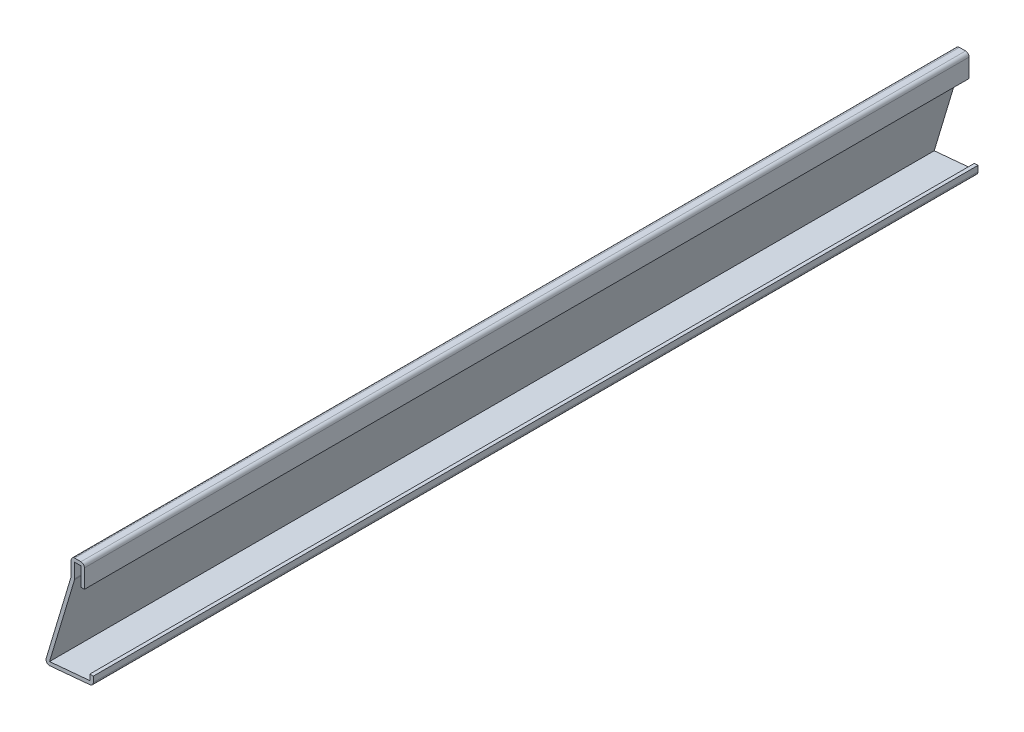
SolidWorks part; units mm, degrees
ref_plane "Front Plane" through (0, 0, 0) normal (0, 0, 1) x (1, 0, 0)
ref_plane "Top Plane" through (0, 0, 0) normal (0, 1, 0) x (1, 0, 0)
ref_plane "Right Plane" through (0, 0, 0) normal (1, 0, 0) x (0, 0, -1)
sketch "Sketch1" plane through (0, 0, 0) normal (0, 0, 1) x (1, 0, 0)
  line L0 (0, 4.7625) -> (0, 1.5875)
  line L1 (0, 1.5875) -> (-17.4625, 0)
  line L2 (-17.4625, 0) -> (-7.9375, 31.75)
  line L3 (-7.9375, 31.75) -> (-7.9375, 38.1)
  line L4 (-7.9375, 38.1) -> (-3.175, 38.1)
  line L5 (-3.175, 38.1) -> (-3.175, 30.1625)
  point P3 (0, 0)
extrude "Extrude-Thin1" add sketch "Sketch1" against normal blind 317.5 thin
fillet "Fillet1" radius 1.27 5 edges at (0, 1.5875, -158.75) (-17.4625, 0, -158.75) (-6.6675, 31.5636, -158.75) (-7.9375, 38.1, -158.75) (-3.175, 38.1, -158.75)
equation "\"D1@Extrude-Thin1\"=\"D5@Sketch1\"*10"
